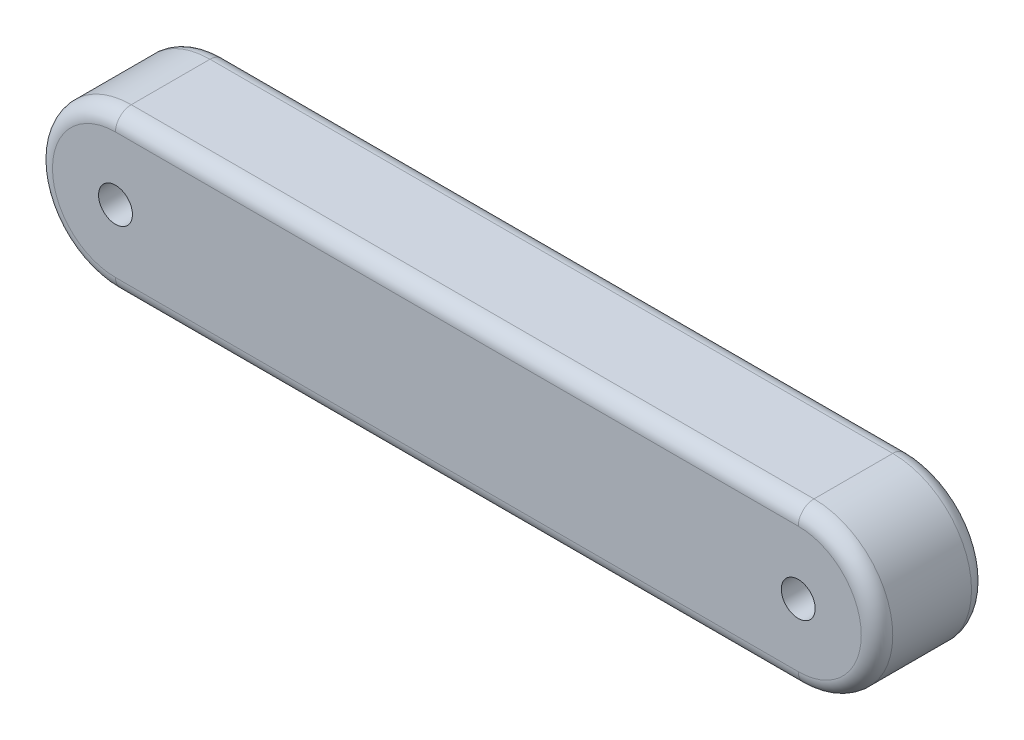
SolidWorks part; units mm, degrees
ref_plane "Front Plane" through (0, 0, 0) normal (0, 0, 1) x (1, 0, 0)
ref_plane "Top Plane" through (0, 0, 0) normal (0, 1, 0) x (1, 0, 0)
ref_plane "Right Plane" through (0, 0, 0) normal (1, 0, 0) x (0, 0, -1)
sketch "Sketch1" plane through (0, 0, 0) normal (0, 0, 1) x (1, 0, 0)
  line L0 (0, 10) -> (0, -10) construction
  line L1 (-43.345, -10) -> (43.345, -10)
  line L3 (-43.345, 10) -> (43.345, 10)
  line L5 (-43.345, -10) -> (43.345, 10) construction
  line L6 (-43.345, 10) -> (43.345, -10) construction
  arc A0 (-43.345, -10) -> (-43.345, 10) centre (-43.345, 0) cw
  circle A1 centre (-43.345, 0) radius 2.15
  arc A2 (43.345, 10) -> (43.345, -10) centre (43.345, 0) cw
  circle A3 centre (43.345, 0) radius 2.15
  point P0 (0, 0)
  dimension "D1" = 4.3
  dimension "D3" = 86.69
  dimension "D2" = 20
extrude "Boss-Extrude1" add sketch "Sketch1" along normal blind 14
ref_plane "Plane1" through (0, 0, 7) normal (0, 0, -1) x (-1, 0, 0)
fillet "Fillet1" radius 2 8 edges at (53.345, 0, 14) (0, -10, 14) (-53.345, 0, 14) (53.345, 0, 0) (0, -10, 0) (-53.345, 0, 0) (0, 10, 14) (0, 10, 0)
